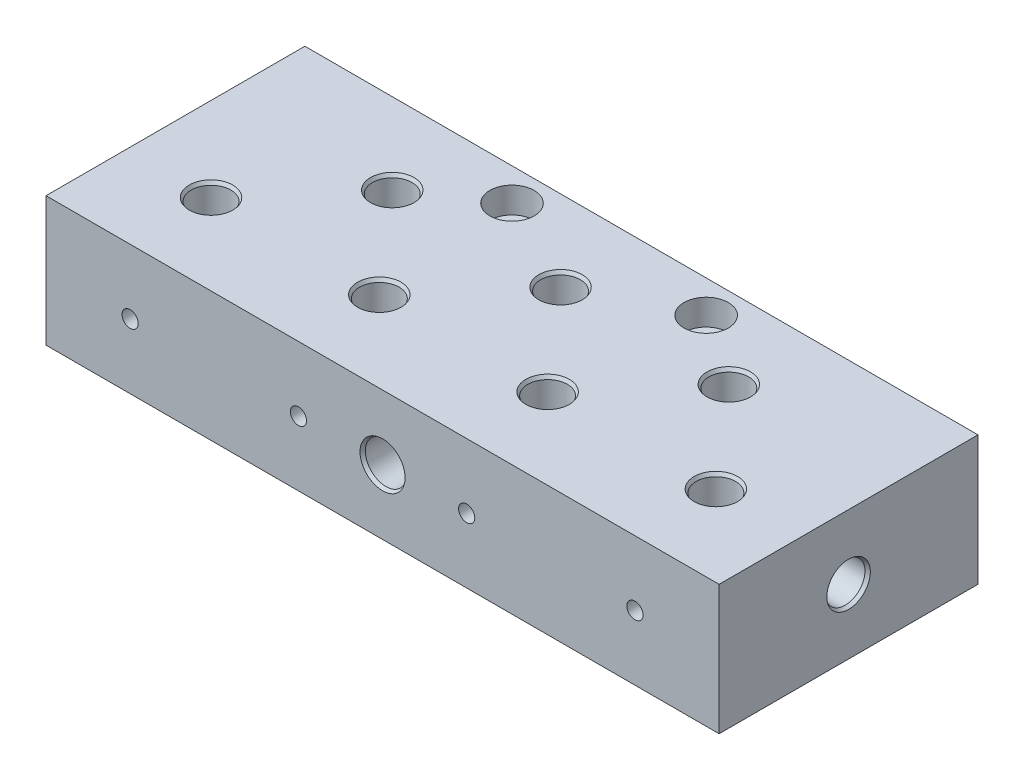
SolidWorks part; units mm, degrees
material "PC High Viscosity"
ref_plane "Front Plane" through (0, 0, 0) normal (0, 0, 1) x (1, 0, 0)
ref_plane "Top Plane" through (0, 0, 0) normal (0, 1, 0) x (1, 0, 0)
ref_plane "Right Plane" through (0, 0, 0) normal (1, 0, 0) x (0, 0, -1)
sketch "Sketch1" plane through (0, 0, 0) normal (0, 1, 0) x (1, 0, 0)
  line L1 (0, 0) -> (132.08, 0)
  line L2 (0, 0) -> (0, 50.8)
  line L3 (0, 50.8) -> (132.08, 50.8)
  line L4 (132.08, 0) -> (132.08, 50.8)
  dimension "D1" = 132.08
  dimension "D2" = 50.8
extrude "Boss-Extrude1" add sketch "Sketch1" along normal blind 25.4
sketch "Sketch2" plane through (0, 25.4, 0) normal (0, 1, 0) x (1, 0, 0)
  line L0 (132.08, 50.8) -> (0, 50.8) construction
  line L2 (0, 50.8) -> (0, 0) construction
  line L3 (132.08, 0) -> (132.08, 50.8) construction
  circle A0 centre (66.04, 34.925) radius 3.8862
  circle A2 centre (99.06, 34.925) radius 3.8862
  circle A3 centre (33.02, 34.925) radius 3.8862
  circle A4 centre (49.53, 15.875) radius 3.8862
  circle A5 centre (82.55, 15.875) radius 3.8862
  circle A6 centre (115.57, 15.875) radius 3.8862
  circle A7 centre (16.51, 15.875) radius 3.8862
  point P9 (66.04, 50.8)
  dimension "D1" = 33.02
  dimension "D2" = 33.02
  dimension "D3" = 0
  dimension "D4" = 16.51
  dimension "D5" = 16.51
  dimension "D6" = 16.51
  dimension "D7" = 16.51
  dimension "D8" = 16.51
  dimension "D9" = 7.7724
  dimension "D10" = 7.7724
  dimension "D11" = 19.05
  dimension "D12" = 19.05
  dimension "D13" = 19.05
  dimension "D14" = 19.05
  dimension "D15" = 15.875
  dimension "D17" = 15.875
  dimension "D18" = 16.51
  dimension "D19" = 16.51
  dimension "D16" = 15.875
extrude "Cut-Extrude1" cut sketch "Sketch2" against normal blind 12.7
sketch "Sketch3" plane through (0, 0, 0) normal (0, 0, 1) x (1, 0, 0)
  line L0 (0, 25.4) -> (0, 0) construction
  line L1 (0, 25.4) -> (132.08, 25.4) construction
  circle A0 centre (16.51, 12.7) radius 1.5875
  circle A1 centre (33.02, 12.7) radius 1.5875
  circle A2 centre (49.53, 12.7) radius 1.5875
  circle A3 centre (66.04, 12.7) radius 1.5875
  circle A4 centre (82.55, 12.7) radius 1.5875
  circle A5 centre (99.06, 12.7) radius 1.5875
  circle A6 centre (115.57, 12.7) radius 1.5875
  dimension "D1" = 16.51
  dimension "D2" = 16.51
  dimension "D3" = 16.51
  dimension "D4" = 16.51
  dimension "D5" = 16.51
  dimension "D6" = 16.51
  dimension "D7" = 16.51
  dimension "D8" = 12.7
  dimension "D9" = 12.7
  dimension "D10" = 12.7
  dimension "D11" = 12.7
  dimension "D12" = 12.7
  dimension "D13" = 12.7
  dimension "D14" = 12.7
extrude "Cut-Extrude2" cut sketch "Sketch3" against normal blind 25.4 contours A0 | A2 | A4 | A6
sketch "Sketch4" plane through (0, 0, 0) normal (0, 0, 1) x (1, 0, 0)
  line L0 (0, 25.4) -> (132.08, 25.4) construction
  circle A0 centre (33.02, 12.7) radius 1.5875
  circle A1 centre (66.04, 12.7) radius 1.5875
  circle A2 centre (99.06, 12.7) radius 1.5875
  circle A3 centre (16.51, 12.7) radius 1.5875 construction
  circle A4 centre (49.53, 12.7) radius 1.5875 construction
  circle A5 centre (82.55, 12.7) radius 1.5875 construction
  dimension "D1" = 16.51
  dimension "D2" = 16.51
  dimension "D3" = 16.51
  dimension "D4" = 12.7
  dimension "D5" = 12.7
  dimension "D6" = 12.7
sketch "Sketch5" plane through (0, 0, -50.8) normal (0, 0, -1) x (-1, 0, 0)
  line L0 (-95.1738, 12.7) -> (-102.9462, 12.7) construction
  line L1 (-62.1538, 12.7) -> (-69.9262, 12.7) construction
  line L2 (-29.1338, 12.7) -> (-36.9062, 12.7) construction
  circle A0 centre (-99.06, 12.7) radius 1.5875
  circle A1 centre (-66.04, 12.7) radius 1.5875
  circle A2 centre (-33.02, 12.7) radius 1.5875
extrude "Cut-Extrude4" cut sketch "Sketch5" against normal blind 25.4
sketch "Sketch6" plane through (132.08, 0, 0) normal (1, 0, 0) x (0, 0, -1)
  circle A0 centre (25.4, 12.7) radius 1.5875
extrude "Cut-Extrude5" cut sketch "Sketch6" against normal through all
sketch "Sketch7" plane through (132.08, 0, 0) normal (1, 0, 0) x (0, 0, -1)
  circle A0 centre (25.4, 12.7) radius 3.8862
extrude "Cut-Extrude6" cut sketch "Sketch7" against normal blind 12.7
sketch "Sketch8" plane through (0, 0, 0) normal (-1, 0, 0) x (0, 0, 1)
  circle A0 centre (-25.4, 12.7) radius 3.8862
extrude "Cut-Extrude7" cut sketch "Sketch8" against normal blind 12.7
sketch "Sketch9" plane through (0, 0, 0) normal (0, 0, 1) x (1, 0, 0)
  circle A0 centre (66.04, 12.7) radius 1.5875
extrude "Cut-Extrude8" cut sketch "Sketch9" against normal blind 25.4
sketch "Sketch10" plane through (0, 0, 0) normal (0, 0, 1) x (1, 0, 0)
  circle A0 centre (66.04, 12.7) radius 4.0386
extrude "Cut-Extrude9" cut sketch "Sketch10" against normal blind 12.7
sketch "Sketch11" plane through (0, 0, 0) normal (0, -1, 0) x (1, 0, 0)
  circle A0 centre (66.04, -25.4) radius 3.8862
extrude "Cut-Extrude10" cut sketch "Sketch11" against normal blind 12.7
sketch "Sketch12" plane through (0, 25.4, 0) normal (0, 1, 0) x (1, 0, 0)
  line L0 (132.08, 50.8) -> (0, 50.8) construction
  circle A0 centre (46.99, 44.45) radius 2.4892
  circle A1 centre (85.09, 44.45) radius 2.4892
  circle A2 centre (66.04, 34.925) radius 3.8862 construction
  dimension "D1" = 4.9784
  dimension "D2" = 4.9784
  dimension "D3" = 38.1
  dimension "D4" = 19.05
  dimension "D5" = 6.35
hole_wizard "CBORE for #10 Socket Head Cap Screw1" positions "Sketch13" profile "Sketch14" counterbore size "#10" standard "ANSI Inch"
sketch "Sketch13" plane through (0, 25.4, 0) normal (0, 1, 0) x (1, 0, 0)
  point P0 (46.99, 44.45)
  point P3 (85.09, 44.45)
sketch "Sketch14" plane through (46.99, 25.4, -44.45) normal (1, 0, 0) x (0, 0, 1)
  line L0 (0, 0) -> (0, 19.2757)
  line L1 (0, 19.2757) -> (2.4892, 17.78)
  line L2 (2.4892, 17.78) -> (2.4892, 5.08)
  line L3 (2.4892, 5.08) -> (4.3434, 5.08)
  line L4 (4.3434, 5.08) -> (4.3434, 0)
  line L5 (4.3434, 0) -> (0, 0)
  line L10 (0, 19.2757) -> (-2.4892, 17.78) construction
  line L11 (0, -6.35) -> (0, 107.95) construction
  dimension "Hole Dia." = 4.9784
  dimension "Hole Depth" = 17.78
  dimension "C'Bore Dia." = 8.6868
  dimension "C'Bore Depth" = 5.08
  dimension "Drill Angle" = 118
chamfer "Chamfer1" distance 0.381 angle 60 11 edges at (66.04, 0, -29.2862) (0, 12.7, -21.5138) (132.08, 12.7, -29.2862) (70.0786, 12.7, 0) (115.57, 25.4, -11.9888) (99.06, 25.4, -31.0388) (82.55, 25.4, -11.9888) (66.04, 25.4, -31.0388) (49.53, 25.4, -11.9888) (33.02, 25.4, -31.0388) (16.51, 25.4, -11.9888)
